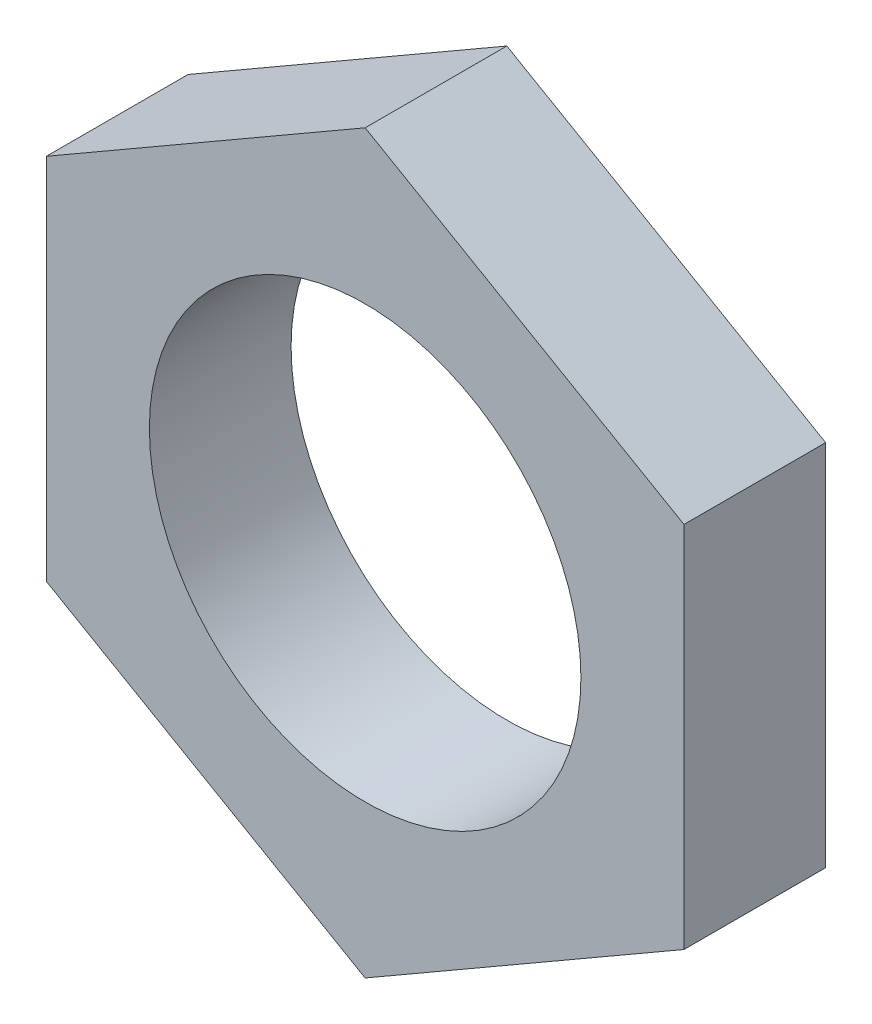
SolidWorks part; units mm, degrees
ref_plane "Front Plane" through (0, 0, 0) normal (0, 0, 1) x (1, 0, 0)
ref_plane "Top Plane" through (0, 0, 0) normal (0, 1, 0) x (1, 0, 0)
ref_plane "Right Plane" through (0, 0, 0) normal (1, 0, 0) x (0, 0, -1)
sketch "Sketch1" plane through (0, 0, 0) normal (0, 0, 1) x (1, 0, 0)
  line L1 (4.95, 2.8579) -> (0, 5.7158)
  line L2 (0, 5.7158) -> (-4.95, 2.8579)
  line L3 (-4.95, 2.8579) -> (-4.95, -2.8579)
  line L4 (-4.95, -2.8579) -> (0, -5.7158)
  line L5 (0, -5.7158) -> (4.95, -2.8579)
  line L6 (4.95, -2.8579) -> (4.95, 2.8579)
  circle A0 centre (0, 0) radius 4.95 construction
  circle A1 centre (0, 0) radius 3.35
  dimension "D2" = 6.7
  dimension "D1" = 9.9
extrude "Boss-Extrude1" add sketch "Sketch1" along normal blind 2.2
cosmetic thread "Cosmetic Thread1" parameters "D2"=8
